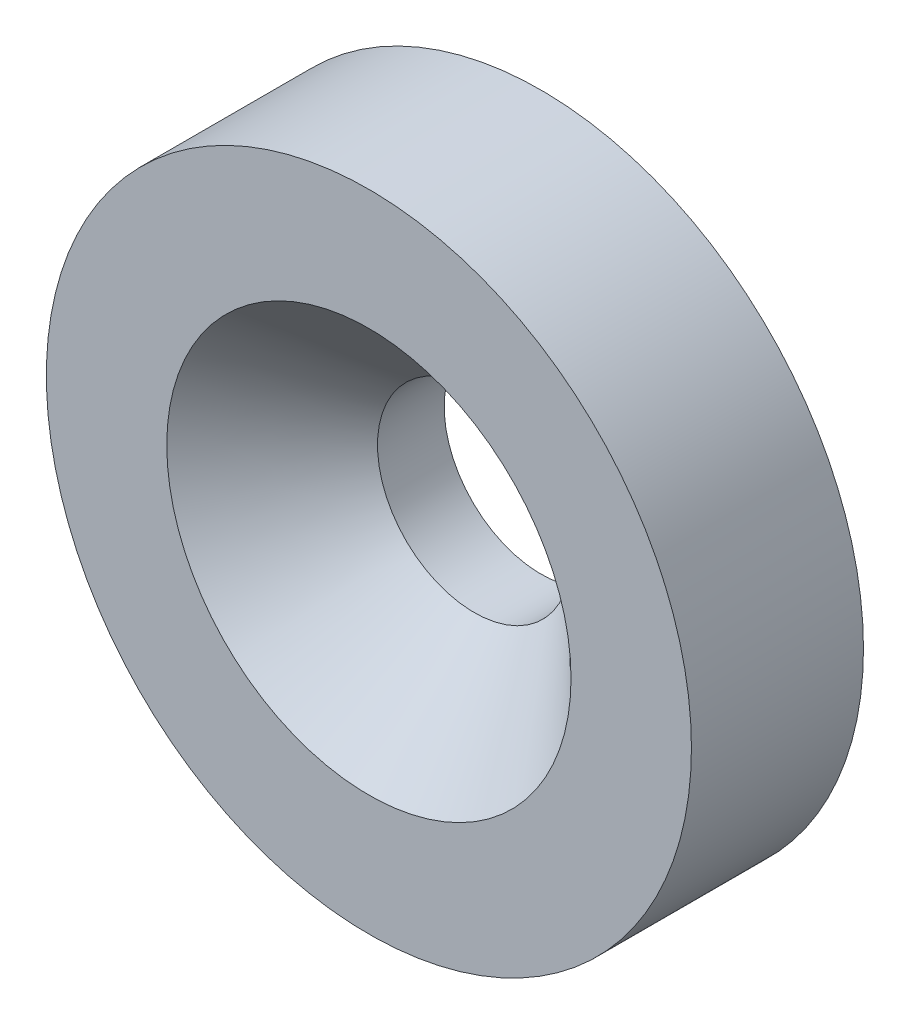
SolidWorks part; units mm, degrees
material "AISI 1020"
ref_plane "Front Plane" through (0, 0, 0) normal (0, 0, 1) x (1, 0, 0)
ref_plane "Top Plane" through (0, 0, 0) normal (0, 1, 0) x (1, 0, 0)
ref_plane "Right Plane" through (0, 0, 0) normal (1, 0, 0) x (0, 0, -1)
sketch "Sketch2" plane through (0, 0, 0) normal (0, 0, 1) x (1, 0, 0)
  circle A0 centre (0, 0) radius 7.5
  point P3 (0, 0)
  dimension "D1" = 15
extrude "Boss-Extrude1" add sketch "Sketch2" against normal blind 4
sketch "Sketch5" plane through (0, 0, 0) normal (0, 0, 1) x (1, 0, 0)
  point P0 (0, 0)
hole_wizard "CSK for M4 Flat Head Machine Screw1" positions "Sketch7" profile "Sketch6" countersink size "M4" standard "ANSI Metric" end condition through all
sketch "Sketch7" plane through (0, 0, 0) normal (0, 0, 1) x (1, 0, 0)
  point P0 (0, 0)
sketch "Sketch6" plane through (0, 0, 0) normal (1, 0, 0) x (0, -1, 0)
  line L0 (0, 0) -> (0, 4)
  line L1 (0, 4) -> (2.25, 4)
  line L2 (2.25, 4) -> (2.25, 2.45)
  line L3 (2.25, 2.45) -> (4.7, 0)
  line L5 (4.7, 0) -> (0, 0)
  line L6 (-2.25, 2.45) -> (-4.7, 0) construction
  line L11 (0, -6.35) -> (0, 107.95) construction
  dimension "Thru Hole Dia." = 4.5
  dimension "Thru Hole Depth" = 4
  dimension "Near C'Sink Dia." = 9.4
  dimension "Near C'Sink Angle" = 90
